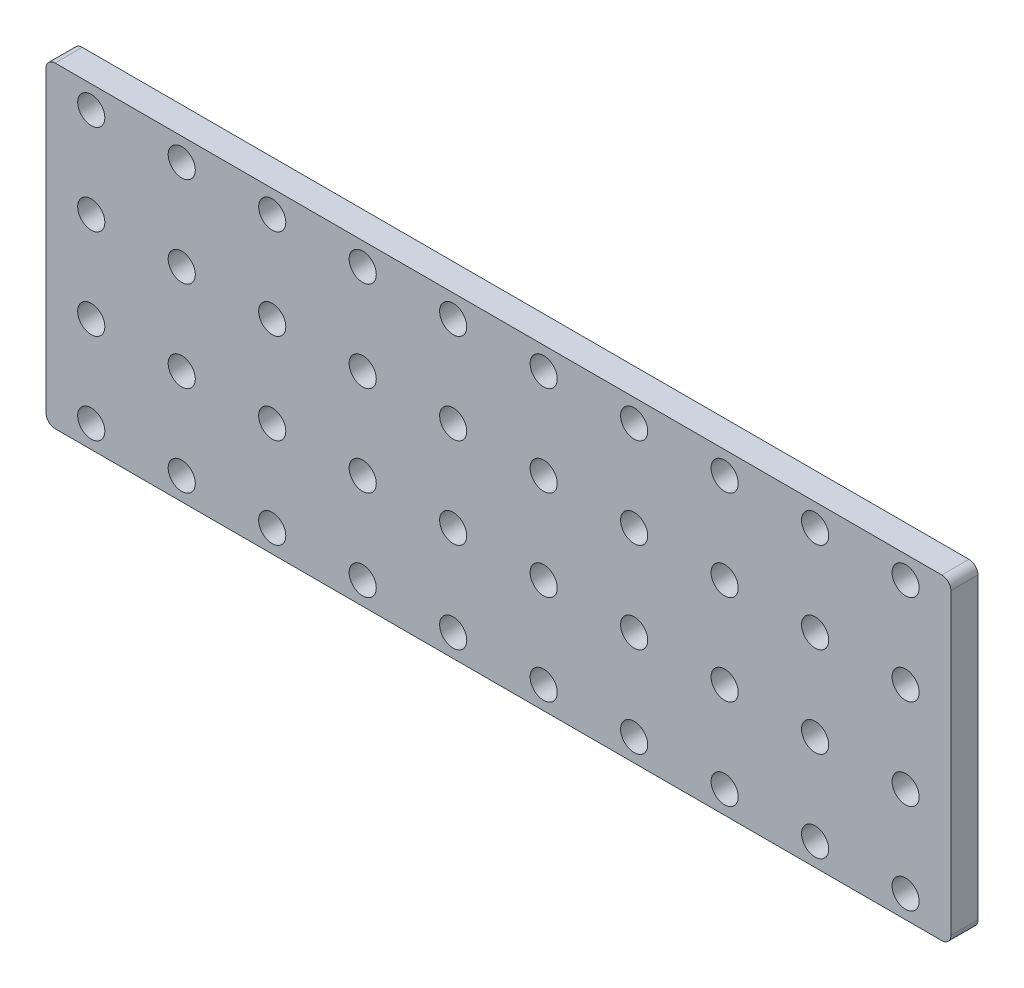
SolidWorks part; units mm, degrees
ref_plane "Plan de face" through (0, 0, 0) normal (0, 0, 1) x (1, 0, 0)
ref_plane "Plan de dessus" through (0, 0, 0) normal (0, 1, 0) x (1, 0, 0)
ref_plane "Plan de droite" through (0, 0, 0) normal (1, 0, 0) x (0, 0, -1)
sketch "Esquisse1" plane through (0, 0, 0) normal (0, 0, 1) x (1, 0, 0)
  line L1 (0, 0) -> (100, 0)
  line L2 (0, 0) -> (0, 35)
  line L3 (0, 35) -> (100, 35)
  line L4 (100, 0) -> (100, 35)
  dimension "D1" = 100
  dimension "D2" = 35
extrude "Boss.-Extru.1" add sketch "Esquisse1" along normal blind 3
sketch "Esquisse2" plane through (0, 0, 3) normal (0, 0, 1) x (1, 0, 0)
  line L0 (100, 35) -> (0, 35) construction
  line L1 (100, 0) -> (100, 35) construction
  circle A0 centre (95, 32.5) radius 1.5
  circle A1 centre (85, 32.5) radius 1.5
  circle A2 centre (75, 32.5) radius 1.5
  circle A3 centre (65, 32.5) radius 1.5
  circle A4 centre (55, 32.5) radius 1.5
  circle A5 centre (45, 32.5) radius 1.5
  circle A6 centre (35, 32.5) radius 1.5
  circle A7 centre (25, 32.5) radius 1.5
  circle A8 centre (15, 32.5) radius 1.5
  circle A9 centre (5, 32.5) radius 1.5
  circle A10 centre (85, 22.5) radius 1.5
  circle A11 centre (75, 22.5) radius 1.5
  circle A12 centre (65, 22.5) radius 1.5
  circle A13 centre (55, 22.5) radius 1.5
  circle A14 centre (45, 22.5) radius 1.5
  circle A15 centre (35, 22.5) radius 1.5
  circle A16 centre (25, 22.5) radius 1.5
  circle A17 centre (15, 22.5) radius 1.5
  circle A18 centre (5, 22.5) radius 1.5
  circle A19 centre (85, 12.5) radius 1.5
  circle A20 centre (75, 12.5) radius 1.5
  circle A21 centre (65, 12.5) radius 1.5
  circle A22 centre (55, 12.5) radius 1.5
  circle A23 centre (45, 12.5) radius 1.5
  circle A24 centre (35, 12.5) radius 1.5
  circle A25 centre (25, 12.5) radius 1.5
  circle A26 centre (15, 12.5) radius 1.5
  circle A27 centre (5, 12.5) radius 1.5
  circle A28 centre (85, 2.5) radius 1.5
  circle A29 centre (75, 2.5) radius 1.5
  circle A30 centre (65, 2.5) radius 1.5
  circle A31 centre (55, 2.5) radius 1.5
  circle A32 centre (45, 2.5) radius 1.5
  circle A33 centre (35, 2.5) radius 1.5
  circle A34 centre (25, 2.5) radius 1.5
  circle A35 centre (15, 2.5) radius 1.5
  circle A36 centre (5, 2.5) radius 1.5
  circle A37 centre (95, 22.5) radius 1.5
  circle A38 centre (95, 12.5) radius 1.5
  circle A39 centre (95, 2.5) radius 1.5
  dimension "D1" = 2.5
  dimension "D2" = 3
  dimension "D3" = 5
  dimension "D4" = 10
  dimension "D5" = 4
extrude "Enlèv. mat.-Extru.1" cut sketch "Esquisse2" against normal blind 3
fillet "Congé1" radius 1 4 edges at (0, 35, 1.5) (0, 0, 1.5) (100, 0, 1.5) (100, 35, 1.5)
